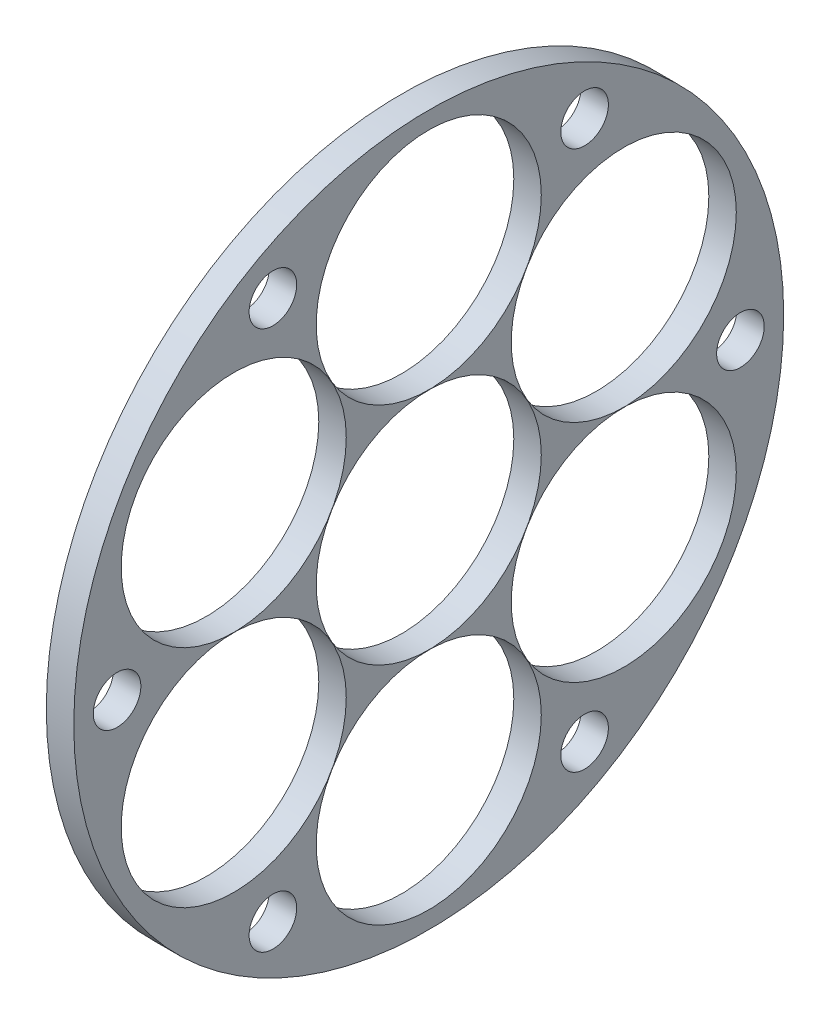
SolidWorks part; units mm, degrees
ref_plane "Front Plane" through (0, 0, 0) normal (0, 0, 1) x (1, 0, 0)
ref_plane "Top Plane" through (0, 0, 0) normal (0, 1, 0) x (1, 0, 0)
ref_plane "Right Plane" through (0, 0, 0) normal (1, 0, 0) x (0, 0, -1)
sketch "Sketch1" plane through (0, 0, 0) normal (1, 0, 0) x (0, 0, -1)
  circle A0 centre (0, 0) radius 41
  point P0 (0, 0)
  dimension "D1" = 82
extrude "Boss-Extrude1" add sketch "Sketch1" along normal blind 3.175
sketch "Sketch2" plane through (3.175, 0, 0) normal (1, 0, 0) x (0, 0, -1)
  line L0 (0, 41) -> (0, -41) construction
  line L1 (-41, 0) -> (41, 0) construction
  line L2 (0, 0) -> (-20.5, 35.507) construction
  circle A0 centre (0, 0) radius 13
  circle A1 centre (0, 26.01) radius 13
  circle A2 centre (22.5253, 13.005) radius 13
  circle A3 centre (22.5253, -13.005) radius 13
  circle A4 centre (0, -26.01) radius 13
  circle A5 centre (-22.5253, -13.005) radius 13
  circle A6 centre (-22.5253, 13.005) radius 13
  circle A7 centre (-18, 31.1769) radius 2.75
  circle A8 centre (0, 0) radius 41 construction
  circle A9 centre (18, 31.1769) radius 2.75
  circle A10 centre (36, 0) radius 2.75
  circle A11 centre (18, -31.1769) radius 2.75
  circle A12 centre (-18, -31.1769) radius 2.75
  circle A13 centre (-36, 0) radius 2.75
  point P18 (0, 0)
  point P38 (0, 0)
  dimension "D1" = 6
  dimension "D3" = 26
  dimension "D4" = 26
  dimension "D5" = 5.5
  dimension "D2" = 26.01
  dimension "D6" = 36
  dimension "D7" = 30
  dimension "D8" = 6
extrude "Cut-Extrude1" cut sketch "Sketch2" against normal blind 25
